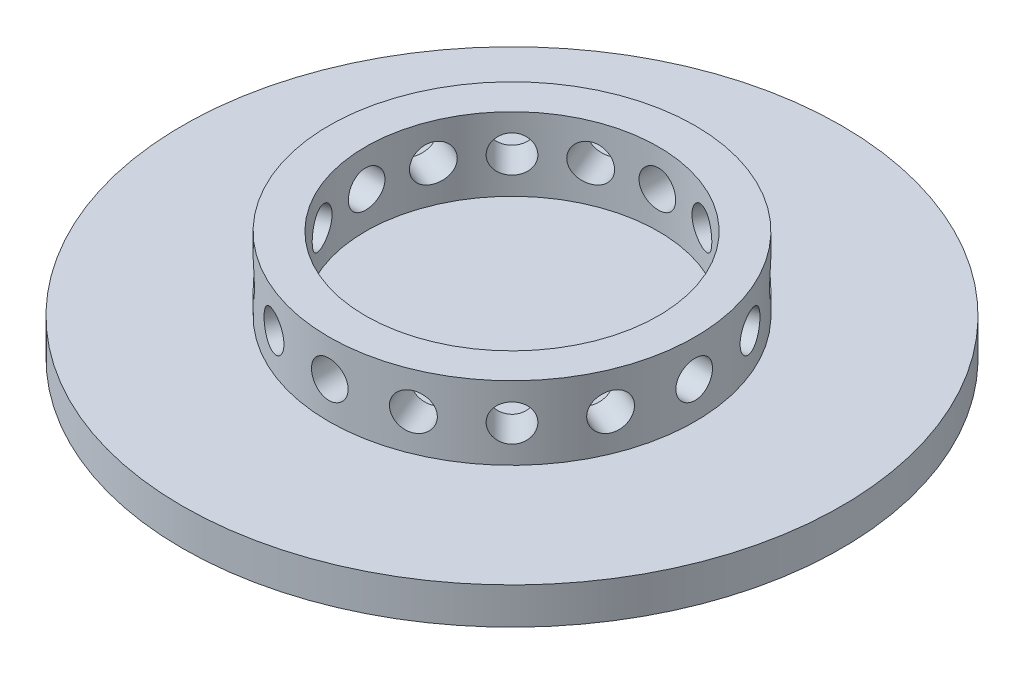
SolidWorks part; units mm, degrees
ref_plane "Front Plane" through (0, 0, 0) normal (0, 0, 1) x (1, 0, 0)
ref_plane "Top Plane" through (0, 0, 0) normal (0, 1, 0) x (1, 0, 0)
ref_plane "Right Plane" through (0, 0, 0) normal (1, 0, 0) x (0, 0, -1)
sketch "Sketch1" plane through (0, 0, 0) normal (0, 0, 1) x (1, 0, 0)
  line L0 (0, 0) -> (-52.0065, 0)
  line L1 (-57.15, 0) -> (-57.15, 6.35)
  line L2 (-57.15, 6.35) -> (-31.75, 6.35)
  line L3 (-31.75, 6.35) -> (-31.75, 19.05)
  line L4 (-31.75, 19.05) -> (-25.4, 19.05)
  line L5 (-25.4, 19.05) -> (-25.4, 6.35)
  line L6 (-25.4, 6.35) -> (0, 6.35)
  line L7 (0, 6.35) -> (0, 0)
  line L8 (-57.15, 0) -> (-55.5625, 0)
  line L9 (-55.5625, 0) -> (-55.5625, 2.54)
  line L10 (-55.5625, 2.54) -> (-52.0065, 2.54)
  line L11 (-52.0065, 2.54) -> (-52.0065, 0)
  dimension "D1" = 57.15
  dimension "D2" = 31.75
  dimension "D3" = 6.35
  dimension "D4" = 6.35
  dimension "D5" = 12.7
  dimension "D6" = 2.54
  dimension "D7" = 3.556
  dimension "D8" = 1.5875
revolve "Revolve1" add sketch "Sketch1" angle 360 about L7
ref_plane "Plane1" through (31.75, 0, 0) normal (1, 0, 0) x (0, 0, -1)
hole_wizard "1/4 (0.25) Diameter Hole1" positions "Sketch2" profile "Sketch3" hole size "1/4" standard "ANSI Inch"
sketch "Sketch2" plane through (31.75, 0, 0) normal (1, 0, 0) x (0, 0, -1)
  point P0 (0, 12.7)
  dimension "D1" = 12.7
sketch "Sketch3" plane through (31.75, 12.7, 0) normal (0, 1, 0) x (0, 0, -1)
  line L0 (0, 0) -> (0, 33.6567)
  line L1 (0, 33.6567) -> (3.175, 31.749)
  line L2 (3.175, 31.749) -> (3.175, 0)
  line L5 (3.175, 0) -> (0, 0)
  line L10 (0, 33.6567) -> (-3.175, 31.749) construction
  line L11 (0, -6.35) -> (0, 107.95) construction
  dimension "Hole Dia." = 6.35
  dimension "Hole Depth" = 31.749
  dimension "Drill Angle" = 118
pattern_circular "CirPattern1" count 16 over 360 about axis through (0, 6.35, 0) along (0, 1, 0) of "1/4 (0.25) Diameter Hole1"
